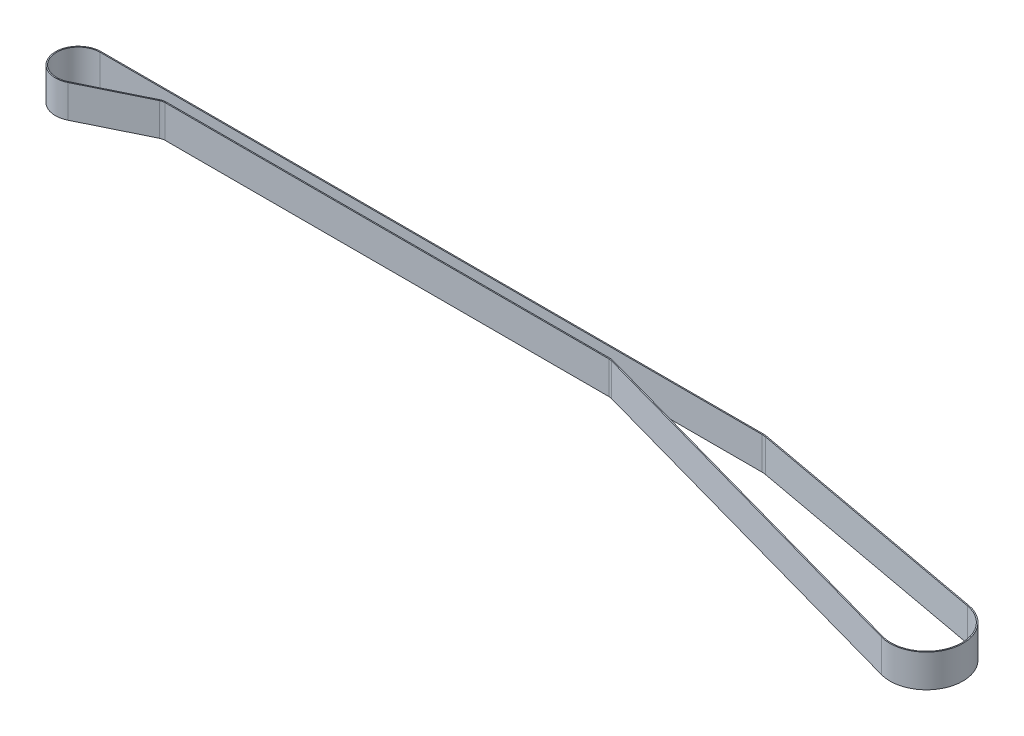
SolidWorks part; units mm, degrees
ref_plane "Front Plane" through (0, 0, 0) normal (0, 0, 1) x (1, 0, 0)
ref_plane "Top Plane" through (0, 0, 0) normal (0, 1, 0) x (1, 0, 0)
ref_plane "Right Plane" through (0, 0, 0) normal (1, 0, 0) x (0, 0, -1)
sketch "Sketch1" plane through (0, 0, 0) normal (0, 1, 0) x (1, 0, 0)
  line L20 (-899.1951, 417.7464) -> (-595.2139, 417.7453)
  line L21 (-660.366, 412.6321) -> (-864.1951, 412.6321)
  line L22 (-899.1951, 418.2464) -> (-595.2139, 418.2443)
  line L23 (-660.366, 413.132) -> (-864.1951, 413.132)
  line L24 (-593.3193, 418.072) -> (-479.6518, 397.2194)
  line L25 (-479.9116, 396.7592) -> (-593.4093, 417.5812)
  line L26 (-487.1661, 364.6079) -> (-659.0251, 412.4489)
  line L27 (-894.7959, 398.766) -> (-866.6147, 412.5712)
  line L28 (-866.3947, 412.1222) -> (-894.5759, 398.317)
  line L29 (-658.8911, 412.9305) -> (-487.0458, 365.0934)
  arc A24 (-899.195, 418.2464) -> (-894.5759, 398.317) centre (-899.1951, 407.7464) ccw
  arc A25 (-864.1951, 412.6321) -> (-866.3947, 412.1222) centre (-864.1951, 407.6321) ccw
  arc A26 (-487.0458, 365.0934) -> (-479.9116, 396.7592) centre (-482.6879, 380.7481) ccw
  circle A27 centre (-618.9568, 407.7443) radius 10.001 construction
  circle A28 centre (-673.9569, 407.6321) radius 5 construction
  arc A29 (-899.1951, 417.7464) -> (-894.7959, 398.766) centre (-899.1951, 407.7464) ccw
  arc A30 (-864.1951, 413.132) -> (-866.6147, 412.5712) centre (-864.1951, 407.632) ccw
  circle A31 centre (-673.9569, 407.632) radius 5.4999 construction
  circle A32 centre (-618.9569, 407.7443) radius 10.5 construction
  arc A33 (-487.1661, 364.6079) -> (-479.6518, 397.2194) centre (-482.6742, 380.7443) ccw
  arc A34 (-593.3193, 418.072) -> (-595.2139, 418.2443) centre (-595.2139, 407.7443) ccw
  arc A35 (-593.4093, 417.5812) -> (-595.2139, 417.7453) centre (-595.2139, 407.7443) ccw
  circle A36 centre (-604.2024, 380.7443) radius 7 construction
  circle A37 centre (-604.2024, 380.7443) radius 7.5 construction
  arc A40 (-658.8911, 412.9305) -> (-660.366, 413.132) centre (-660.366, 407.6321) ccw
  arc A41 (-659.0251, 412.4489) -> (-660.366, 412.6321) centre (-660.366, 407.6321) ccw
extrude "Boss-Extrude1" add sketch "Sketch1" along normal blind 15 contours A41 L26 A33 L24 A34 L22 A24 L28 A25 L21 L29 A40 L23 A30 L27 A29 L20 A35 L25 A26
